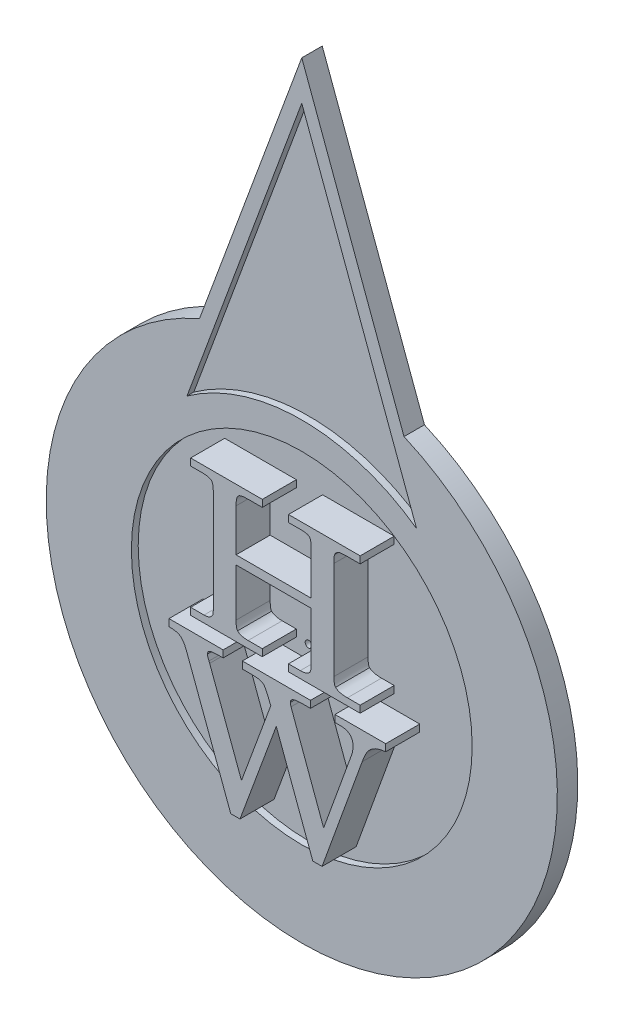
SolidWorks part; units mm, degrees
ref_plane "Front Plane" through (0, 0, 0) normal (0, 0, 1) x (1, 0, 0)
ref_plane "Top Plane" through (0, 0, 0) normal (0, 1, 0) x (1, 0, 0)
ref_plane "Right Plane" through (0, 0, 0) normal (1, 0, 0) x (0, 0, -1)
sketch "Sketch1" plane through (0, 0, 0) normal (0, 0, 1) x (1, 0, 0)
  line L0 (0, 0) -> (0, 75) construction
  line L1 (0, 75) -> (15, 34.3693)
  line L2 (0, 75) -> (-15, 34.3693)
  arc A0 (-15, 34.3693) -> (15, 34.3693) centre (0, 0) ccw
  dimension "D1" = 75
  dimension "D2" = 75
  dimension "D3" = 30
extrude "Boss-Extrude1" add sketch "Sketch1" along normal blind 3
sketch "Sketch2" plane through (0, 0, 3) normal (0, 0, 1) x (1, 0, 0)
  circle A0 centre (0, 0) radius 25
  dimension "D1" = 50
extrude "Cut-Extrude1" cut sketch "Sketch2" against normal blind 1
sketch "Sketch3" plane through (0, 0, 2) normal (0, 0, 1) x (1, 0, 0)
  circle A0 centre (0, 0) radius 0.5
  dimension "D1" = 1
extrude "Cut-Extrude2" cut sketch "Sketch3" against normal through all
sketch "Sketch4" plane through (0, 0, 3) normal (0, 0, 1) x (1, 0, 0)
  line L2 (13.1238, 33.6767) -> (-1.8762, 74.3073)
  line L3 (16.8404, 23.6093) -> (0, 69.2252)
  line L5 (1.8762, 74.3073) -> (-13.1238, 33.6767)
  line L6 (0, 69.2252) -> (-16.8404, 23.6093)
  circle A2 centre (0, 0) radius 29
  arc A3 (16.8404, 23.6093) -> (-16.8404, 23.6093) centre (0, 0) ccw
  dimension "D1" = 2
  dimension "D2" = 2
  dimension "D3" = 4
extrude "Cut-Extrude3" cut sketch "Sketch4" against normal blind 1
sketch "Sketch5" plane through (0, 0, 2) normal (0, 0, 1) x (1, 0, 0)
  line L0 (-20, 0) -> (20, 0) construction
  line L1 (-16, -22) -> (8, -22) construction
  line L2 (0, 0) -> (0, -28.1737) construction
  text T0 "H" font "Century Schoolbook" height 20
  text T1 "W" font "Century Schoolbook" height 20
  point P3 (0, 0)
  dimension "D1" = 40
  dimension "D2" = 24
  dimension "D3" = 22
  dimension "D4" = 16
extrude "Boss-Extrude2" add sketch "Sketch5" along normal blind 5 separate body
